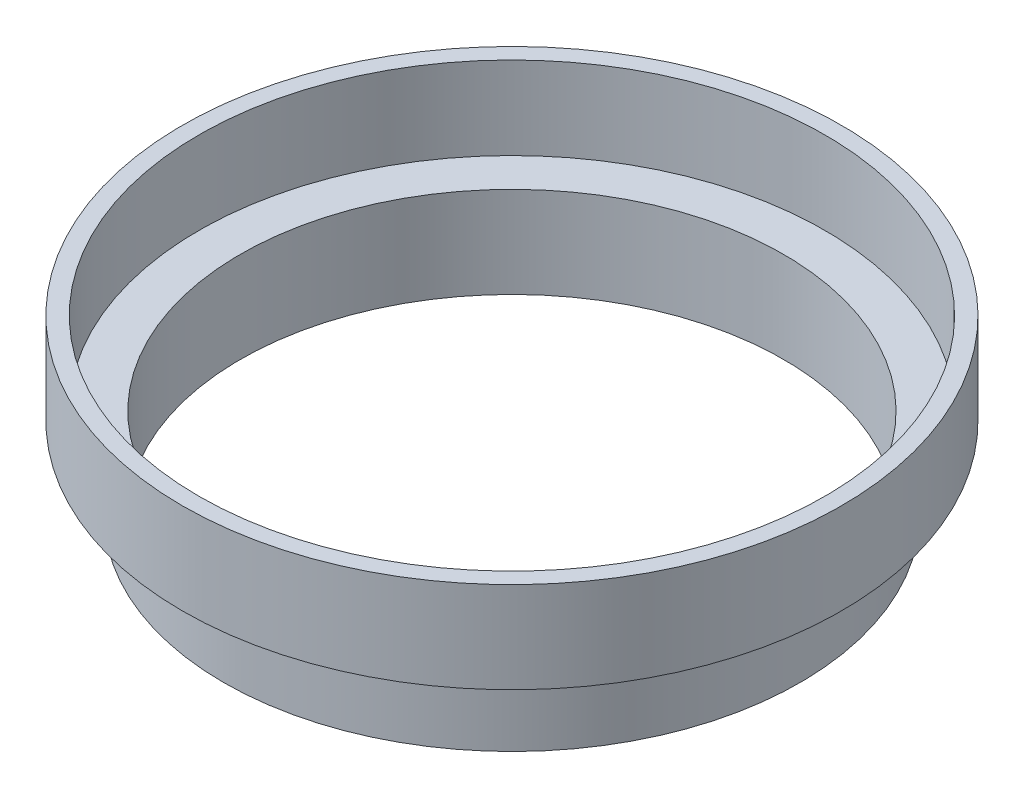
SolidWorks part; units mm, degrees
material "1060 Alloy"
ref_plane "Front Plane" through (0, 0, 0) normal (0, 0, 1) x (1, 0, 0)
ref_plane "Top Plane" through (0, 0, 0) normal (0, 1, 0) x (1, 0, 0)
ref_plane "Right Plane" through (0, 0, 0) normal (1, 0, 0) x (0, 0, -1)
sketch "Sketch1" plane through (0, 0, 0) normal (0, 1, 0) x (1, 0, 0)
  circle A0 centre (0, 0) radius 41.6814
  circle A2 centre (0, 0) radius 44.2214
  dimension "D1" = 83.3628
  dimension "D2" = 2.54
extrude "Boss-Extrude1" add sketch "Sketch1" along normal blind 12.7
sketch "Sketch2" plane through (0, 12.7, 0) normal (0, 1, 0) x (1, 0, 0)
  circle A0 centre (0, 0) radius 50.5714
  circle A1 centre (0, 0) radius 44.2214 construction
  circle A2 centre (0, 0) radius 41.6814
  circle A3 centre (0, 0) radius 41.6814 construction
  dimension "D1" = 6.35
extrude "Boss-Extrude2" add sketch "Sketch2" along normal blind 1.27
sketch "Sketch3" plane through (0, 13.97, 0) normal (0, 1, 0) x (1, 0, 0)
  circle A0 centre (0, 0) radius 48.0314
  circle A1 centre (0, 0) radius 50.5714
  circle A2 centre (0, 0) radius 50.5714 construction
  dimension "D1" = 2.54
extrude "Boss-Extrude3" add sketch "Sketch3" along normal blind 12.7
